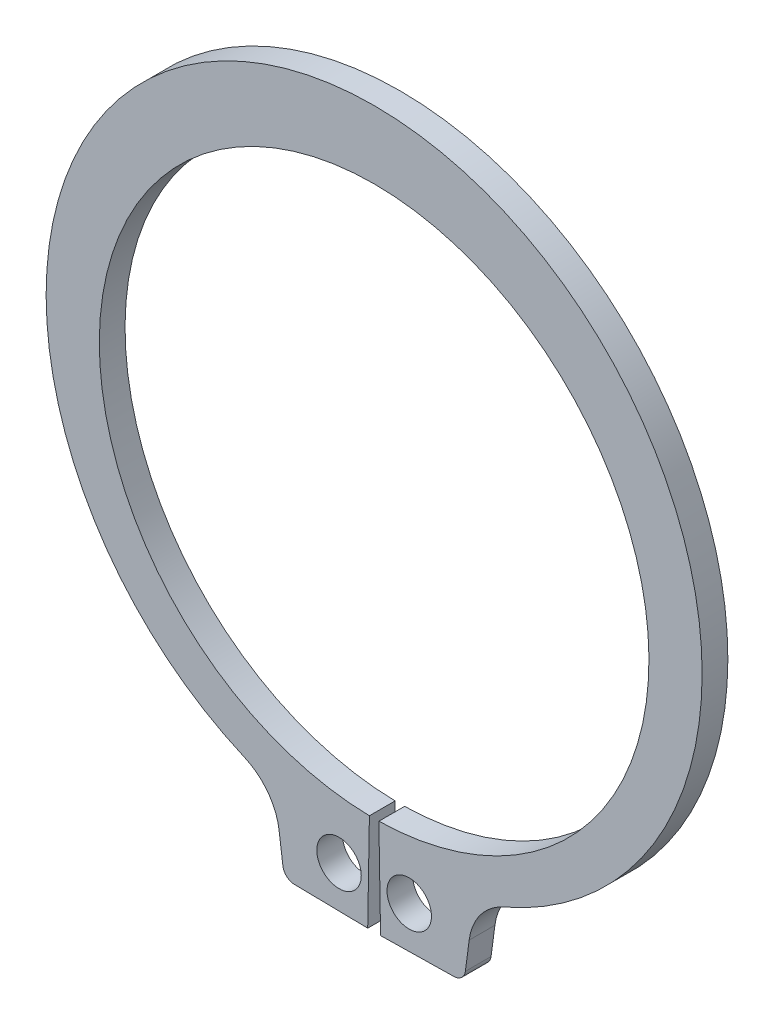
SolidWorks part; units mm, degrees
ref_plane "Plane1" through (0, 0, 0) normal (0, 0, 1) x (1, 0, 0)
ref_plane "Plane2" through (0, 0, 0) normal (0, 1, 0) x (1, 0, 0)
ref_plane "Plane3" through (0, 0, 0) normal (1, 0, 0) x (0, 0, -1)
other "Configuration Table"
sketch "Clipboard" plane through (0, 0, 0) normal (0, 0, 1) x (1, 0, 0)
  line L0 (0, 0) -> (2.9, 0)
  line L1 (0, 0) -> (0, 1.7)
  line L2 (0, 0) -> (0, -4.2)
  circle A0 centre (0, 0) radius 0.95
  circle A1 centre (0, 0) radius 12.5
  dimension "HoleDia" = 1.9
  dimension "ShaftDia" = 25
  dimension "LargeSection" = 2.9
  dimension "SmallSection" = 1.7
  dimension "LugSection" = 4.2
sketch "BodySke" plane through (0, 0, 0) normal (0, 0, 1) x (1, 0, 0)
  line L0 (-1.5431, 0) -> (1.5431, 0) construction
  line L1 (0, 0) -> (0, 14.65) construction
  line L2 (0.2026, -11.7483) -> (0.275, -15.9476)
  line L3 (-0.2026, -11.7483) -> (-0.275, -15.9476)
  line L4 (0, 0) -> (6.5413, -14.547) construction
  line L5 (0, 0) -> (-6.5413, -14.547) construction
  line L6 (0.275, -15.9476) -> (3.4129, -15.8935)
  line L7 (4.063, -14.2207) -> (3.9, -15.4589)
  line L8 (-4.063, -14.2207) -> (-3.9, -15.4589)
  line L9 (-0.275, -15.9476) -> (-3.4129, -15.8935)
  circle A0 centre (0, 0) radius 11.75 construction
  arc A1 (0.2026, -11.7483) -> (-0.2026, -11.7483) centre (0, 0) ccw
  arc A2 (5.516, -12.2669) -> (-5.516, -12.2669) centre (0, 0.6264) ccw construction
  arc A3 (0.275, -15.9476) -> (3.9942, -15.4418) centre (0, 0) ccw construction
  arc A4 (5.5517, -12.2515) -> (4.063, -14.2207) centre (6.5413, -14.547) ccw
  arc A5 (-4.063, -14.2207) -> (-5.5517, -12.2515) centre (-6.5413, -14.547) ccw
  arc A6 (-3.9942, -15.4418) -> (-0.275, -15.9476) centre (0, 0) ccw construction
  arc A7 (5.5517, -12.2515) -> (-5.5517, -12.2515) centre (0, 0.6264) ccw
  arc A8 (-4.1437, -13.6081) -> (4.1437, -13.6081) centre (0, 0) ccw construction
  circle A9 centre (1.5, -14.1457) radius 0.95
  circle A10 centre (-1.5, -14.1457) radius 0.95
  arc A11 (3.9, -15.4589) -> (3.4129, -15.8935) centre (3.4043, -15.3936) cw
  arc A12 (-3.9, -15.4589) -> (-3.4129, -15.8935) centre (-3.4043, -15.3936) ccw
  point P28 (3.8991, -15.4661)
  point P31 (-3.8991, -15.4661)
  dimension "GrooveDia" = 23.5
  dimension "LugRad" = 15.95
  dimension "HoleOffsetRad" = 14.225
  dimension "HoleDia" = 1.9
  dimension "D3" = 0.5
  dimension "LargeRad" = 14.65
  dimension "SmallRad" = 13.45
  dimension "SmallAngle" = 48.424
  dimension "D2" = 15
  dimension "HoleSpacing" = 3
  dimension "Gap" = 0.55
extrude "Body" add sketch "BodySke" against normal blind 1.1
sketch "NotSke" plane through (0, 0, 0) normal (0, 0, 1) x (1, 0, 0)
  line L0 (1.5, -13.1957) -> (1.5, -15.0957)
  line L1 (1.5, -15.0957) -> (-1.5, -15.0957)
  line L2 (-1.5, -15.0957) -> (-1.5, -13.1957)
  line L3 (-1.5, -13.1957) -> (1.5, -13.1957)
  circle A0 centre (1.5, -14.1457) radius 0.95 construction
  circle A1 centre (-1.5, -14.1457) radius 0.95 construction
extrude "Notch" [suppressed] cut sketch "NotSke" against normal through all
equation "' \"ShaftDia@Clipboard\" = 4"
equation "' \"Thickness@Body\" = 0.25"
equation "' \"GrooveDia@BodySke\" = 3.8"
equation "' \"LugSection@Clipboard\" = 1.35"
equation "' \"LargeSection@Clipboard\" = 0.65"
equation "' \"SmallSection@Clipboard\" = 0.4"
equation "' \"HoleDia@Clipboard\" = 0.6"
equation "' \"ShaftDia@Clipboard\" = 15"
equation "' \"Thickness@Body\" = 0.9"
equation "' \"GrooveDia@BodySke\" = 14.15"
equation "' \"LugSection@Clipboard\" = 2.8"
equation "' \"LargeSection@Clipboard\" = 1.8"
equation "' \"SmallSection@Clipboard\" = 1.05"
equation "' \"HoleDia@Clipboard\" = 1.2"
equation "\"Gap@BodySke\" =  \"Thickness@Body\" / 2"
equation "\"LargeRad@BodySke\" =  \"GrooveDia@BodySke\" / 2 +  \"LargeSection@Clipboard\""
equation "\"SmallRad@BodySke\" =  \"GrooveDia@BodySke\" / 2 +  \"SmallSection@Clipboard\""
equation "\"LugRad@BodySke\" = \"GrooveDia@BodySke\" / 2 + \"LugSection@Clipboard\""
equation "\"HoleOffsetRad@BodySke\" = (  \"ShaftDia@Clipboard\" / 2 + \"LugRad@BodySke\" ) / 2"
equation "\"HoleSpacing@BodySke\" = \"Gap@BodySke\"  * 2 +  \"HoleDia@Clipboard\""
equation "\"HoleDia@BodySke\" =  \"HoleDia@Clipboard\""
equation "\"SmallAngle@BodySke\" = atn(\"HoleSpacing@BodySke\" / 2 / sqr(\"HoleOffsetRad@BodySke\"  * \"HoleOffsetRad@BodySke\" - (\"HoleSpacing@BodySke\" / 2) * (\"HoleSpacing@BodySke\" / 2) ))  * 8 * ( 180 / 3.141593)"
